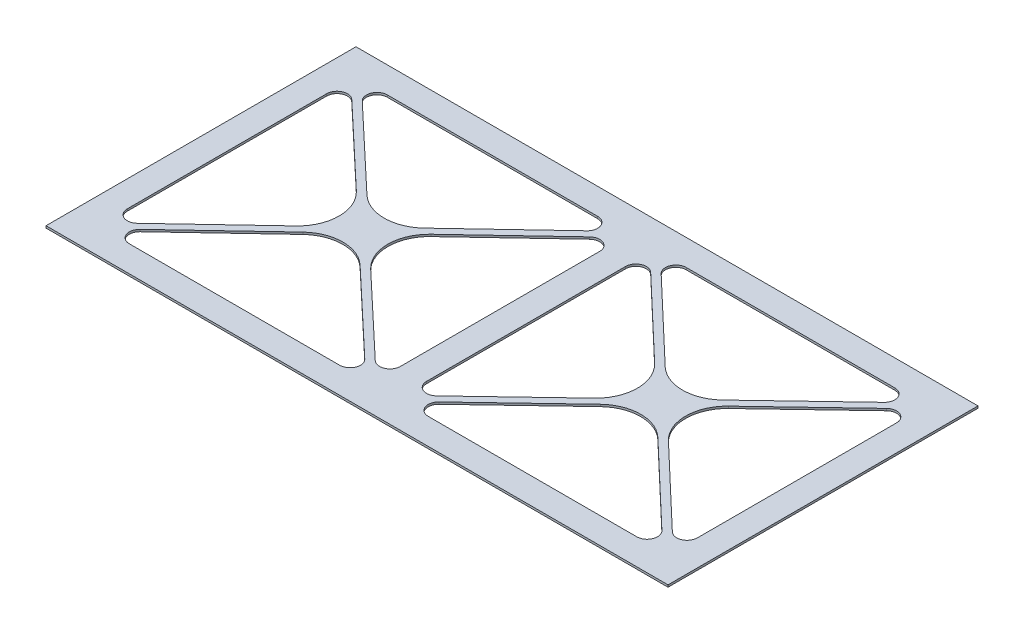
SolidWorks part; units mm, degrees
ref_plane "Front Plane" through (0, 0, 0) normal (0, 0, 1) x (1, 0, 0)
ref_plane "Top Plane" through (0, 0, 0) normal (0, 1, 0) x (1, 0, 0)
ref_plane "Right Plane" through (0, 0, 0) normal (1, 0, 0) x (0, 0, -1)
sketch "Sketch1" plane through (0, 0, 0) normal (0, 1, 0) x (1, 0, 0)
  line L0 (10, 107.2) -> (60.4403, 59.6)
  line L1 (0, 0) -> (239.2, 0)
  line L2 (0, 0) -> (0, 119.2)
  line L3 (0, 119.2) -> (239.2, 119.2)
  line L4 (239.2, 0) -> (239.2, 119.2)
  line L5 (12, 109.2) -> (113, 109.2)
  line L6 (10, 107.2) -> (10, 12)
  line L7 (12, 10) -> (113, 10)
  line L8 (115, 107.2) -> (115, 12)
  line L9 (127, 109.2) -> (227.2, 109.2)
  line L10 (125, 107.2) -> (125, 12)
  line L11 (127, 10) -> (227.2, 10)
  line L12 (229.2, 107.2) -> (229.2, 12)
  line L13 (12, 109.2) -> (62.5, 61.5437)
  line L14 (113, 109.2) -> (62.5, 61.5437)
  line L15 (115, 107.2) -> (64.5597, 59.6)
  line L16 (60.4403, 59.6) -> (10, 12)
  line L17 (62.5, 57.6563) -> (113, 10)
  line L18 (64.5597, 59.6) -> (115, 12)
  line L19 (62.5, 57.6563) -> (12, 10)
  line L20 (125, 107.2) -> (175.0486, 59.6)
  line L21 (127, 109.2) -> (177.1, 61.5511)
  line L22 (227.2, 109.2) -> (177.1, 61.5511)
  line L23 (229.2, 107.2) -> (179.1514, 59.6)
  line L24 (175.0486, 59.6) -> (125, 12)
  line L25 (177.1, 57.6489) -> (227.2, 10)
  line L26 (177.1, 57.6489) -> (127, 10)
  line L27 (179.1514, 59.6) -> (229.2, 12)
  dimension "D1" = 119.2
  dimension "D2" = 239.2
  dimension "D3" = 10
  dimension "D4" = 10
  dimension "D5" = 10
  dimension "D6" = 115
  dimension "D7" = 10
  dimension "D8" = 10
  dimension "D9" = 10
  dimension "D10" = 10
extrude "Boss-Extrude1" add sketch "Sketch1" along normal blind 0.8
fillet "Fillet2" radius 16 8 edges at (60.4403, 0.4, -59.6) (62.5, 0.4, -61.5437) (64.5597, 0.4, -59.6) (62.5, 0.4, -57.6563) (177.1, 0.4, -61.5511) (177.1, 0.4, -57.6489) (179.1514, 0.4, -59.6) (175.0486, 0.4, -59.6)
fillet "Fillet3" radius 4 16 edges at (10, 0.4, -12) (12, 0.4, -10) (113, 0.4, -10) (115, 0.4, -12) (115, 0.4, -107.2) (113, 0.4, -109.2) (12, 0.4, -109.2) (10, 0.4, -107.2) (125, 0.4, -12) (127, 0.4, -10) (227.2, 0.4, -10) (229.2, 0.4, -12) (229.2, 0.4, -107.2) (227.2, 0.4, -109.2) (127, 0.4, -109.2) (125, 0.4, -107.2)
